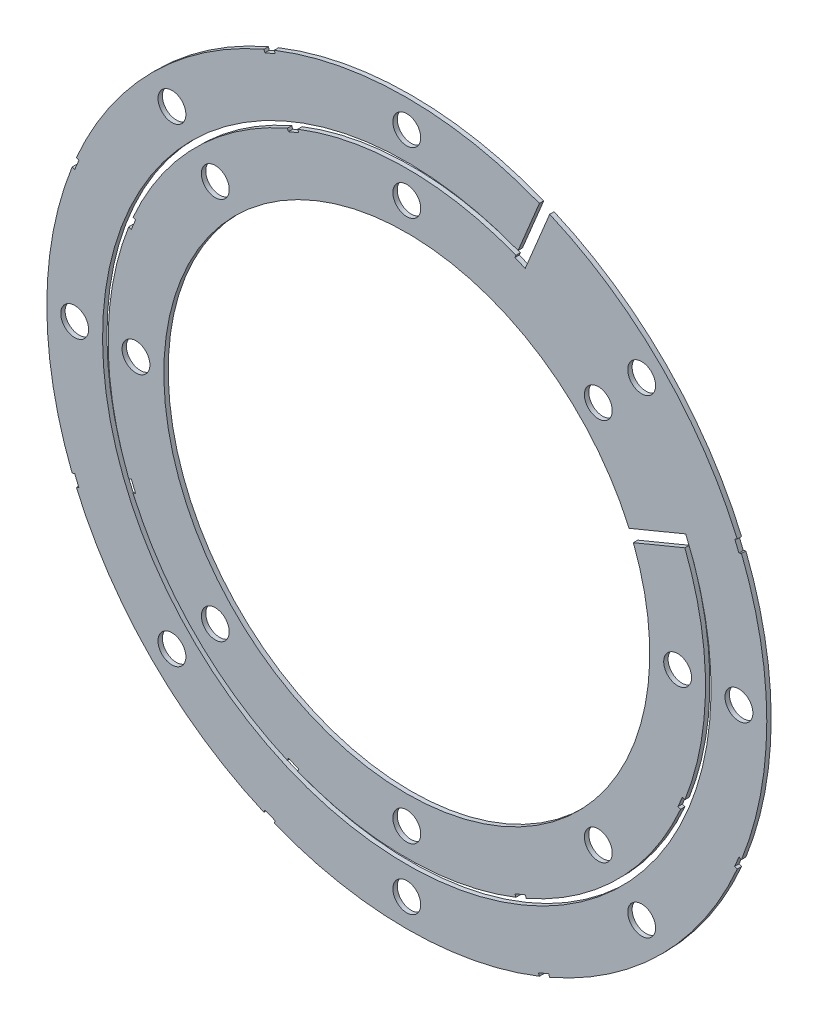
SolidWorks part; units mm, degrees
material "Copper"
ref_plane "Front Plane" through (0, 0, 0) normal (0, 0, 1) x (1, 0, 0)
ref_plane "Top Plane" through (0, 0, 0) normal (0, 1, 0) x (1, 0, 0)
ref_plane "Right Plane" through (0, 0, 0) normal (1, 0, 0) x (0, 0, -1)
sketch "Sketch1" plane through (0, 0, 0) normal (0, 0, 1) x (1, 0, 0)
  line L0 (0, 0) -> (101.6, 0) construction
  line L1 (0, 0) -> (93.8662, 38.8806) construction
  line L2 (0, 0) -> (38.8806, 93.8662) construction
  line L3 (25.3583, 64.5389) -> (30.219, 76.2739)
  line L4 (27.2188, 62.3934) -> (32.5657, 75.3018)
  line L5 (50.6576, 22.3577) -> (63.5669, 27.7049)
  line L6 (51.6296, 20.011) -> (63.3654, 24.8722)
  arc A0 (51.6296, 20.011) -> (50.6576, 22.3577) centre (0, 0) cw
  arc A1 (63.3654, 24.8722) -> (27.2188, 62.3934) centre (0, 0) cw
  arc A2 (63.5669, 27.7049) -> (25.3583, 64.5389) centre (0, 0) cw
  arc A3 (32.5657, 75.3018) -> (30.219, 76.2739) centre (0, 0) cw
  dimension "D4" = 1.27
  dimension "D12" = 1.27
  dimension "D1" = 22.5
  dimension "D2" = 67.5
  dimension "D3" = 1.27
  dimension "D5" = 55.372
  dimension "D11" = 1.27
  dimension "D8" = 12.7
  dimension "D14" = 12.7
  dimension "D6" = 1.27
  dimension "D7" = 1.27
  dimension "D9" = 1.27
  dimension "D10" = 1.27
  dimension "D13" = 1.27
extrude "Boss-Extrude1" add sketch "Sketch1" along normal blind 1
sketch "Sketch2" plane through (0, 0, 1) normal (0, 0, 1) x (1, 0, 0)
  line L0 (0, 0) -> (82.042, 0) construction
  circle A0 centre (61.722, 0) radius 3.175
  circle A2 centre (75.692, 0) radius 3.175
  arc A3 (50.6576, 22.3577) -> (51.6296, 20.011) centre (0, 0) ccw construction
  circle A4 centre (53.5223, -53.5223) radius 3.175
  circle A5 centre (43.644, -43.644) radius 3.175
  circle A6 centre (0, -75.692) radius 3.175
  circle A7 centre (0, -61.722) radius 3.175
  circle A8 centre (-53.5223, -53.5223) radius 3.175
  circle A9 centre (-43.644, -43.644) radius 3.175
  circle A10 centre (-75.692, 0) radius 3.175
  circle A11 centre (-61.722, 0) radius 3.175
  circle A12 centre (-53.5223, 53.5223) radius 3.175
  circle A13 centre (-43.644, 43.644) radius 3.175
  circle A14 centre (0, 75.692) radius 3.175
  circle A15 centre (0, 61.722) radius 3.175
  circle A16 centre (53.5223, 53.5223) radius 3.175
  circle A17 centre (43.644, 43.644) radius 3.175
  arc A19 (30.219, 76.2739) -> (32.5657, 75.3018) centre (0, 0) ccw construction
  point P40 (0, 0)
  point P48 (0, 0)
  dimension "D1" = 6.35
  dimension "D2" = 6.35
  dimension "D3" = 6.35
  dimension "D4" = 13.97
  dimension "D5" = 8
  dimension "D6" = 6.35
  dimension "D7" = 6.35
extrude "Cut-Extrude1" cut sketch "Sketch2" against normal through all
sketch "Sketch3" plane through (0, 0, 1) normal (0, 0, 1) x (1, 0, 0)
  line L0 (0, 0) -> (75.692, 0) construction
  line L1 (0, 0) -> (75.7969, -31.3961) construction
  line L2 (61.8177, -26.9803) -> (62.991, -27.4664)
  line L3 (61.8177, -26.9803) -> (62.7897, -24.6337)
  line L4 (62.991, -27.4664) -> (63.963, -25.1197)
  line L5 (62.7897, -24.6337) -> (63.963, -25.1197)
  line L6 (61.8177, -26.9803) -> (63.963, -25.1197) construction
  line L7 (62.991, -27.4664) -> (62.7897, -24.6337) construction
  line L8 (25.1197, -63.963) -> (27.4664, -62.991)
  line L9 (26.9803, -61.8177) -> (27.4664, -62.991)
  line L10 (24.6337, -62.7897) -> (26.9803, -61.8177)
  line L11 (24.6337, -62.7897) -> (25.1197, -63.963)
  line L12 (-27.4664, -62.991) -> (-25.1197, -63.963)
  line L13 (-24.6337, -62.7897) -> (-25.1197, -63.963)
  line L14 (-26.9803, -61.8177) -> (-24.6337, -62.7897)
  line L15 (-26.9803, -61.8177) -> (-27.4664, -62.991)
  line L16 (-63.963, -25.1197) -> (-62.991, -27.4664)
  line L17 (-61.8177, -26.9803) -> (-62.991, -27.4664)
  line L18 (-62.7897, -24.6337) -> (-61.8177, -26.9803)
  line L19 (-62.7897, -24.6337) -> (-63.963, -25.1197)
  line L20 (-62.991, 27.4664) -> (-63.963, 25.1197)
  line L21 (-62.7897, 24.6337) -> (-63.963, 25.1197)
  line L22 (-61.8177, 26.9803) -> (-62.7897, 24.6337)
  line L23 (-61.8177, 26.9803) -> (-62.991, 27.4664)
  line L24 (-25.1197, 63.963) -> (-27.4664, 62.991)
  line L25 (-26.9803, 61.8177) -> (-27.4664, 62.991)
  line L26 (-24.6337, 62.7897) -> (-26.9803, 61.8177)
  line L27 (-24.6337, 62.7897) -> (-25.1197, 63.963)
  line L28 (27.4664, 62.991) -> (25.1197, 63.963)
  line L29 (24.6337, 62.7897) -> (25.1197, 63.963)
  line L30 (26.9803, 61.8177) -> (24.6337, 62.7897)
  line L31 (26.9803, 61.8177) -> (27.4664, 62.991)
  line L32 (0, 0) -> (62.7897, -24.6337) construction
  line L33 (0, 0) -> (26.9803, -61.8177) construction
  line L34 (32.5657, 75.3018) -> (27.2188, 62.3934) construction
  line L35 (0, 0) -> (75.7969, 31.3961) construction
  line L36 (75.6963, 29.9798) -> (76.8696, 30.4658)
  line L37 (75.6963, 29.9798) -> (74.7243, 32.3264)
  line L38 (76.8696, 30.4658) -> (75.8976, 32.8124)
  line L39 (74.7243, 32.3264) -> (75.8976, 32.8124)
  line L40 (75.6963, 29.9798) -> (75.8976, 32.8124) construction
  line L41 (76.8696, 30.4658) -> (74.7243, 32.3264) construction
  line L42 (75.6963, -29.9798) -> (76.8696, -30.4658)
  line L43 (75.8976, -32.8124) -> (76.8696, -30.4658)
  line L44 (74.7243, -32.3264) -> (75.6963, -29.9798)
  line L45 (74.7243, -32.3264) -> (75.8976, -32.8124)
  line L46 (32.3264, -74.7243) -> (32.8124, -75.8976)
  line L47 (30.4658, -76.8696) -> (32.8124, -75.8976)
  line L48 (29.9798, -75.6963) -> (32.3264, -74.7243)
  line L49 (29.9798, -75.6963) -> (30.4658, -76.8696)
  line L50 (-29.9798, -75.6963) -> (-30.4658, -76.8696)
  line L51 (-32.8124, -75.8976) -> (-30.4658, -76.8696)
  line L52 (-32.3264, -74.7243) -> (-29.9798, -75.6963)
  line L53 (-32.3264, -74.7243) -> (-32.8124, -75.8976)
  line L54 (-74.7243, -32.3264) -> (-75.8976, -32.8124)
  line L55 (-76.8696, -30.4658) -> (-75.8976, -32.8124)
  line L56 (-75.6963, -29.9798) -> (-74.7243, -32.3264)
  line L57 (-75.6963, -29.9798) -> (-76.8696, -30.4658)
  line L58 (-75.6963, 29.9798) -> (-76.8696, 30.4658)
  line L59 (-75.8976, 32.8124) -> (-76.8696, 30.4658)
  line L60 (-74.7243, 32.3264) -> (-75.6963, 29.9798)
  line L61 (-74.7243, 32.3264) -> (-75.8976, 32.8124)
  line L62 (-32.3264, 74.7243) -> (-32.8124, 75.8976)
  line L63 (-30.4658, 76.8696) -> (-32.8124, 75.8976)
  line L64 (-29.9798, 75.6963) -> (-32.3264, 74.7243)
  line L65 (-29.9798, 75.6963) -> (-30.4658, 76.8696)
  line L66 (0, 0) -> (75.6963, 29.9798) construction
  line L67 (0, 0) -> (74.7243, -32.3264) construction
  arc A0 (30.219, 76.2739) -> (32.5657, 75.3018) centre (0, 0) ccw construction
  arc A1 (27.2188, 62.3934) -> (63.3654, 24.8722) centre (0, 0) ccw construction
  point P9 (62.8903, -26.05)
  point P47 (75.7969, 31.3961)
  dimension "D1" = 22.5
  dimension "D2" = 1.27
  dimension "D3" = 2.54
  dimension "D4" = 1.27
  dimension "D5" = 0.635
  dimension "D7" = 45
  dimension "D8" = 0.635
  dimension "D9" = 67.5
  dimension "D10" = 2.54
  dimension "D11" = 22.5
  dimension "D12" = 1.27
  dimension "D13" = 2.54
  dimension "D14" = 0.635
  dimension "D15" = 1.27
  dimension "D17" = 45
  dimension "D18" = 112.5
  dimension "D19" = 0.635
  dimension "D20" = 0.635
  dimension "D21" = 0.635
  dimension "D6" = 7
  dimension "D16" = 7
extrude "Cut-Extrude2" cut sketch "Sketch3" against normal through all
